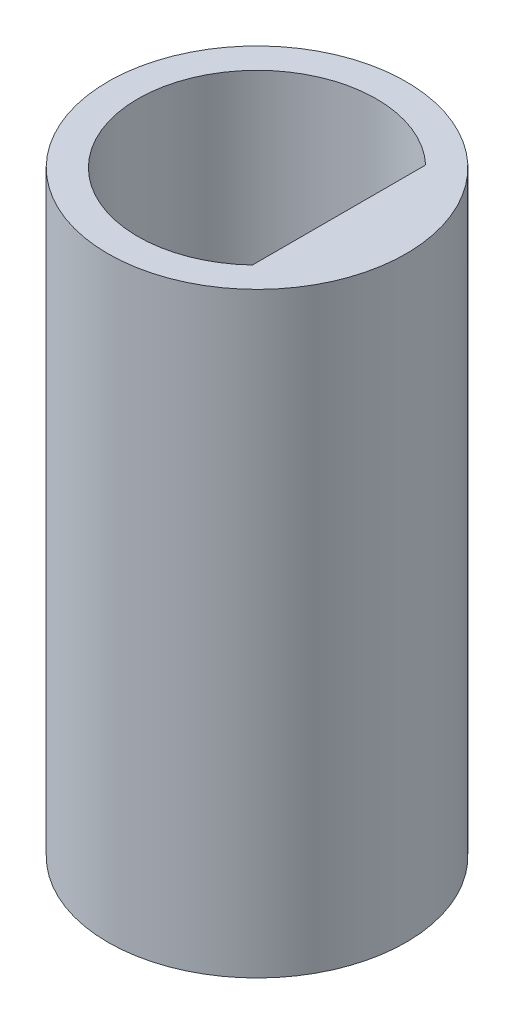
SolidWorks part; units mm, degrees
ref_plane "Front Plane" through (0, 0, 0) normal (0, 0, 1) x (1, 0, 0)
ref_plane "Top Plane" through (0, 0, 0) normal (0, 1, 0) x (1, 0, 0)
ref_plane "Right Plane" through (0, 0, 0) normal (1, 0, 0) x (0, 0, -1)
sketch "Sketch1" plane through (0, 0, 0) normal (0, 1, 0) x (1, 0, 0)
  line L0 (1.1, 1.1619) -> (1.1, -1.1619)
  circle A0 centre (0, 0) radius 2
  arc A1 (1.1, 1.1619) -> (1.1, -1.1619) centre (0, 0) ccw
  dimension "D1" = 4
  dimension "D2" = 3.2
  dimension "D3" = 1.1
extrude "Boss-Extrude1" add sketch "Sketch1" along normal blind 8
